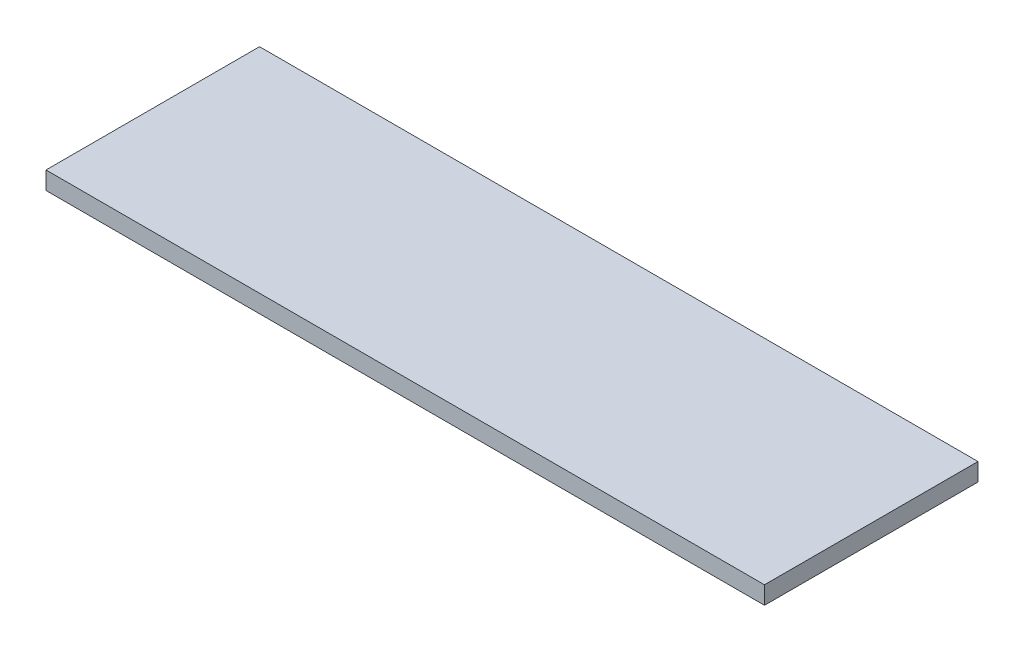
SolidWorks part; units mm, degrees
ref_plane "Front Plane" through (0, 0, 0) normal (0, 0, 1) x (1, 0, 0)
ref_plane "Top Plane" through (0, 0, 0) normal (0, 1, 0) x (1, 0, 0)
ref_plane "Right Plane" through (0, 0, 0) normal (1, 0, 0) x (0, 0, -1)
sketch "Sketch1" plane through (0, 0, 0) normal (0, 1, 0) x (1, 0, 0)
  line L1 (-64.1, 19.05) -> (64.1, 19.05)
  line L2 (-64.1, 19.05) -> (-64.1, -19.05)
  line L3 (-64.1, -19.05) -> (64.1, -19.05)
  line L4 (64.1, 19.05) -> (64.1, -19.05)
  line L5 (-64.1, 19.05) -> (64.1, -19.05) construction
  line L6 (-64.1, -19.05) -> (64.1, 19.05) construction
  point P0 (0, 0)
  dimension "D1" = 128.2
  dimension "D2" = 38.1
extrude "Boss-Extrude1" add sketch "Sketch1" along normal blind 3.175
equation "\"width\"= ( 52mm ) + ( 1.5in * 2 )"
equation "\"length\" = 1.5in"
equation "\"D1@Sketch1\"=\"width\""
equation "\"D2@Sketch1\"=\"length\""
